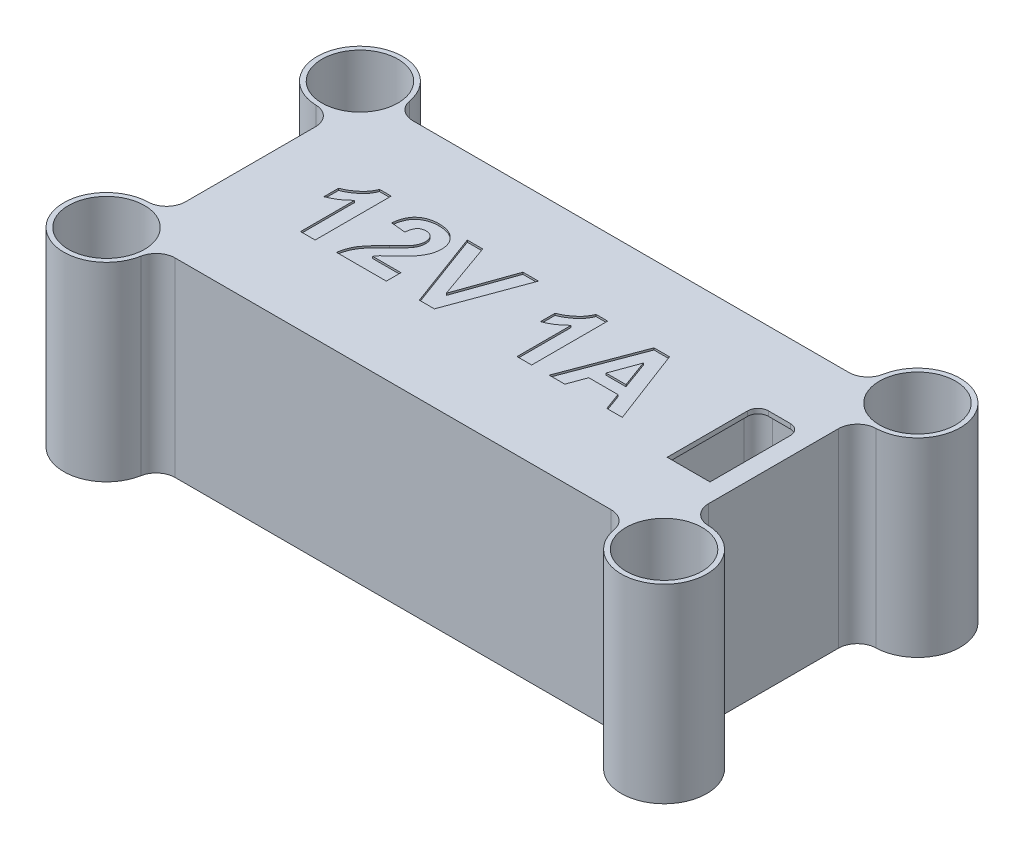
SolidWorks part; units mm, degrees
ref_plane "Front Plane" through (0, 0, 0) normal (0, 0, 1) x (1, 0, 0)
ref_plane "Top Plane" through (0, 0, 0) normal (0, 1, 0) x (1, 0, 0)
ref_plane "Right Plane" through (0, 0, 0) normal (1, 0, 0) x (0, 0, -1)
sketch "Sketch1" plane through (0, 0, 0) normal (0, 1, 0) x (1, 0, 0)
  line L0 (0, 12.5) -> (0, -12.5) construction
  line L1 (-27.5, 12.5) -> (27.5, 12.5)
  line L2 (-27.5, 12.5) -> (-27.5, -12.5)
  line L3 (-27.5, -12.5) -> (27.5, -12.5)
  line L4 (27.5, 12.5) -> (27.5, -12.5)
  line L5 (-27.5, 12.5) -> (27.5, -12.5) construction
  line L6 (-27.5, -12.5) -> (27.5, 12.5) construction
  line L7 (-27.5, 0) -> (27.5, 0) construction
  line L8 (-24.8207, 13.3276) -> (-24.8207, 12.5)
  line L9 (-29.3207, 8.8276) -> (-27.5, 8.8276)
  line L10 (24.8207, 13.3276) -> (24.8207, 12.5)
  line L11 (29.3207, 8.8276) -> (27.5, 8.8276)
  line L12 (29.3207, -8.8276) -> (27.5, -8.8276)
  line L13 (24.8207, -13.3276) -> (24.8207, -12.5)
  line L14 (-24.8207, -13.3276) -> (-24.8207, -12.5)
  line L15 (-29.3207, -8.8276) -> (-27.5, -8.8276)
  circle A0 centre (-29.3207, 13.3276) radius 2
  circle A1 centre (-29.3207, 13.3276) radius 4.5
  circle A2 centre (29.3207, 13.3276) radius 2
  circle A3 centre (29.3207, 13.3276) radius 4.5
  circle A4 centre (29.3207, -13.3276) radius 2
  circle A5 centre (29.3207, -13.3276) radius 4.5
  circle A6 centre (-29.3207, -13.3276) radius 2
  circle A7 centre (-29.3207, -13.3276) radius 4.5
  point P0 (0, 0)
  dimension "D3" = 4
  dimension "D4" = 9
  dimension "D1" = 25
  dimension "D2" = 55
extrude "Boss-Extrude1" add sketch "Sketch1" along normal blind 20 contours A7 L3 A6 L2 | L3 A7 L14 | A7 L2 L3 | L15 A7 L2 | L2 A7 L3 A5 L4 A3 L1 A1 | A1 L9 L2 | A1 L2 A0 L1 | L2 A1 L1 | A1 L1 L8 | L11 A3 L4 | L1 A3 L10 | A3 L4 L1 | A3 L1 A2 L4 | A5 L12 L4 | A5 L3 L13 | L4 A5 L3 | A5 L4 A4 L3
sketch "Sketch2" plane through (0, 20, 0) normal (0, 1, 0) x (1, 0, 0)
  line L0 (0, 12.5) -> (0, -12.5) construction
  line L1 (-24.8207, 12.5) -> (24.8207, 12.5) construction
  line L2 (-24.8207, -12.5) -> (24.8207, -12.5) construction
  line L3 (-27.5, 0) -> (27.5, 0) construction
  line L4 (-27.5, 8.8276) -> (-27.5, -8.8276) construction
  line L5 (27.5, 8.8276) -> (27.5, -8.8276) construction
  circle A0 centre (-29.3207, 13.3276) radius 4
  arc A1 (-24.8207, 13.3276) -> (-29.3207, 8.8276) centre (-29.3207, 13.3276) ccw construction
  circle A2 centre (29.3207, 13.3276) radius 4
  circle A3 centre (29.3207, -13.3276) radius 4
  circle A4 centre (-29.3207, -13.3276) radius 4
  dimension "D1" = 0.5
extrude "Cut-Extrude1" cut sketch "Sketch2" against normal offset from surface (18.5 mm away) 1.5 up to face at (0, 0, 0)
sketch "Sketch3" plane through (0, 20, 0) normal (0, 1, 0) x (1, 0, 0)
  line L0 (-27.5, 0) -> (27.5, 0) construction
  line L1 (-27.5, 8.8276) -> (-27.5, -8.8276) construction
  line L2 (27.5, 8.8276) -> (27.5, -8.8276) construction
  line L3 (23.35, 12.5) -> (23.35, -12.5) construction
  line L4 (-24.8207, 12.5) -> (24.8207, 12.5) construction
  line L5 (-24.8207, -12.5) -> (24.8207, -12.5) construction
  line L7 (22.2, 5.175) -> (24.5, 5.175)
  line L8 (20.7, 3.675) -> (20.7, -5.175)
  line L9 (20.7, -5.175) -> (26, -5.175)
  line L10 (26, 3.675) -> (26, -5.175)
  line L11 (20.7, 5.175) -> (26, -5.175) construction
  line L12 (20.7, -5.175) -> (26, 5.175) construction
  arc A0 (24.5, 5.175) -> (26, 3.675) centre (24.5, 3.675) cw
  arc A1 (22.2, 5.175) -> (20.7, 3.675) centre (22.2, 3.675) ccw
  point P12 (23.35, 0)
  dimension "D4" = 1.5
  dimension "D1" = 1.5
  dimension "D2" = 10.35
  dimension "D3" = 5.3
extrude "Cut-Extrude2" cut sketch "Sketch3" against normal up to next from offset 0.5 offset against normal yes
sketch "Sketch5" plane through (0, 0, 0) normal (0, -1, 0) x (1, 0, 0)
  line L0 (-27.5, 0) -> (-26, 0) construction
  line L1 (26, -11) -> (-26, -11)
  line L2 (26, -11) -> (26, 11)
  line L3 (26, 11) -> (-26, 11)
  line L4 (-26, -11) -> (-26, 11)
  line L5 (26, -11) -> (-26, 11) construction
  line L6 (26, 11) -> (-26, -11) construction
  line L7 (-27.5, -8.8276) -> (-27.5, 8.8276) construction
  line L8 (0, 11) -> (0, 12.5) construction
  line L9 (-24.8207, 12.5) -> (24.8207, 12.5) construction
  line L10 (19.2, 11) -> (19.2, -11)
  line L11 (19.2, 0) -> (20.7, 0) construction
  line L13 (19.2, 6.675) -> (26, 6.675)
  line L14 (23.35, 5.175) -> (23.35, 6.675) construction
  line L16 (19.2, -6.675) -> (26, -6.675)
  line L17 (26, 5.175) -> (20.7, 5.175) construction
  line L18 (20.7, 5.175) -> (20.7, -3.675) construction
  point P0 (0, 0)
  point P28 (0, 0)
  point P29 (0, 0)
  dimension "D1" = 1.5
extrude "Cut-Extrude4" cut sketch "Sketch5" against normal offset from surface (18.5 mm away) 1.5 contours L10 L3 L4 L1 | L10 L13 L2 L3 | L16 L10 L1 L2 up to face at (29.3207, 20, -17.3276)
sketch "Sketch7" plane through (0, 19.5, 0) normal (0, -1, 0) x (1, 0, 0)
  line L8 (25.6, -3.675) -> (25.6, 4.775)
  line L9 (25.6, 4.775) -> (21.1, 4.775)
  line L10 (21.1, 4.775) -> (21.1, -3.675)
  line L11 (22.2, -4.775) -> (24.5, -4.775)
  line L12 (25.6, -3.675) -> (25.6, 4.775)
  line L13 (25.6, 4.775) -> (21.1, 4.775)
  line L14 (21.1, 4.775) -> (21.1, -3.675)
  line L15 (22.2, -4.775) -> (24.5, -4.775)
  arc A4 (21.1, -3.675) -> (22.2, -4.775) centre (22.2, -3.675) ccw
  arc A5 (24.5, -4.775) -> (25.6, -3.675) centre (24.5, -3.675) ccw
  arc A6 (21.1, -3.675) -> (22.2, -4.775) centre (22.2, -3.675) ccw
  arc A7 (24.5, -4.775) -> (25.6, -3.675) centre (24.5, -3.675) ccw
  dimension "D1" = 0.4
extrude "Cut-Extrude6" cut sketch "Sketch7" against normal up to next
sketch "Sketch8" plane through (0, 0, 0) normal (0, -1, 0) x (1, 0, 0)
  line L1 (19.2, 6.675) -> (26, 6.675)
  line L2 (19.2, 6.675) -> (19.2, -6.675)
  line L3 (19.2, -6.675) -> (26, -6.675)
  line L4 (26, 6.675) -> (26, -6.675)
extrude "Cut-Extrude7" cut sketch "Sketch8" against normal offset from surface (8.8 mm away) 10.7 up to face at (23.35, 19.5, -1.3009)
fillet "Fillet1" radius 2 8 edges at (-24.8207, 10, 12.5) (27.5, 10, -8.8276) (27.5, 10, 8.8276) (-24.8207, 10, -12.5) (24.8207, 10, -12.5) (-27.5, 10, 8.8276) (24.8207, 10, 12.5) (-27.5, 10, -8.8276)
sketch "Sketch9" plane through (0, 20, 0) normal (0, 1, 0) x (1, 0, 0)
  line L0 (-27.5, -3.5033) -> (21.1, -3.5033) construction
  line L1 (-27.5, 6.8301) -> (-27.5, -6.8301) construction
  line L3 (21.1, -4.775) -> (21.1, 3.675) construction
  text T0 "12V 1A" font "Arial" height 8
extrude "Cut-Extrude8" cut sketch "Sketch9" against normal blind 0.2
sketch "Sketch10" plane through (0, 8.8, 0) normal (0, -1, 0) x (1, 0, 0)
  line L0 (19.2, 0) -> (20.7, 0) construction
  line L1 (19.2, 6.675) -> (19.2, -6.675) construction
  line L2 (20.7, 5.175) -> (20.7, -3.675) construction
  line L4 (21, -0.75) -> (19.2, -0.75)
  line L5 (21, -0.75) -> (21, 0.75)
  line L6 (21, 0.75) -> (19.2, 0.75)
  line L7 (19.2, -0.75) -> (19.2, 0.75)
  line L8 (21, -0.75) -> (19.2, 0.75) construction
  line L9 (21, 0.75) -> (19.2, -0.75) construction
  point P7 (20.1, 0)
  dimension "D1" = 0.3
  dimension "D2" = 1.5
extrude "Boss-Extrude2" add sketch "Sketch10" along normal blind 1
chamfer "Chamfer1" distance 0.5 angle 45 1 edges at (21, 7.8, 0)
